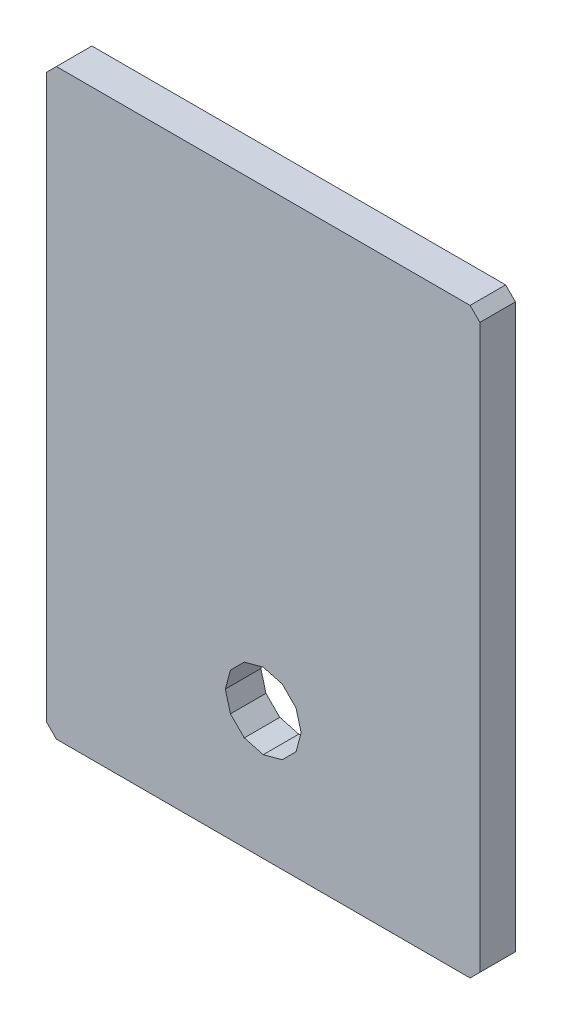
SolidWorks part; units mm, degrees
material "Медь"
ref_plane "Спереди" through (0, 0, 0) normal (0, 0, 1) x (1, 0, 0)
ref_plane "Сверху" through (0, 0, 0) normal (0, 1, 0) x (1, 0, 0)
ref_plane "Справа" through (0, 0, 0) normal (1, 0, 0) x (0, 0, -1)
sketch "Эскиз2" plane through (0, 0, 0) normal (0, 0, 1) x (-1, 0, 0)
  line L0 (9.15, -11.8858) -> (9.15, 11.8858)
  line L1 (9.15, -11.8858) -> (8.7358, -12.3)
  line L2 (8.7358, 12.3) -> (-8.7358, 12.3)
  line L3 (-9.15, -11.8858) -> (-8.7358, -12.3)
  line L4 (-9.15, 11.8858) -> (-9.15, -11.8858)
  line L5 (-9.15, 11.8858) -> (-8.7358, 12.3)
  line L6 (-8.7358, -12.3) -> (8.7358, -12.3)
  line L7 (8.7358, 12.3) -> (9.15, 11.8858)
  line L21 (0, 8.5) -> (-0.8, 8.2856)
  line L22 (-0.8, 8.2856) -> (-1.3856, 7.7)
  line L23 (-1.3856, 7.7) -> (-1.6, 6.9)
  line L24 (-1.6, 6.9) -> (-1.3856, 6.1)
  line L25 (-1.3856, 6.1) -> (-0.8, 5.5144)
  line L26 (-0.8, 5.5144) -> (0, 5.3)
  line L27 (0, 5.3) -> (0.8, 5.5144)
  line L28 (0.8, 5.5144) -> (1.3856, 6.1)
  line L29 (1.3856, 6.1) -> (1.6, 6.9)
  line L30 (1.6, 6.9) -> (1.3856, 7.7)
  line L31 (1.3856, 7.7) -> (0.8, 8.2856)
  line L32 (0.8, 8.2856) -> (0, 8.5)
  point P0 (0, 0)
extrude "Бобышка-Вытянуть3" add sketch "Эскиз2" along normal blind 1.5
